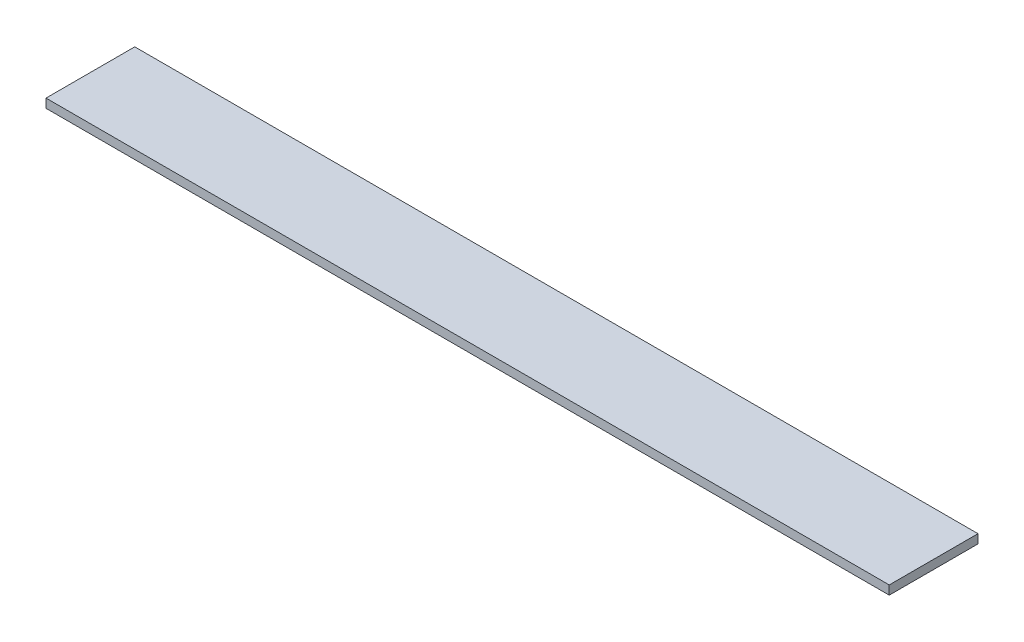
SolidWorks part; units mm, degrees
ref_plane "Face" through (0, 0, 0) normal (0, 0, 1) x (1, 0, 0)
ref_plane "Dessus" through (0, 0, 0) normal (0, 1, 0) x (1, 0, 0)
ref_plane "Droite" through (0, 0, 0) normal (1, 0, 0) x (0, 0, -1)
sketch "Esquisse1" plane through (0, 0, 0) normal (0, 1, 0) x (1, 0, 0)
  line L1 (0, 0) -> (950, 0)
  line L2 (0, 0) -> (0, 100)
  line L3 (0, 100) -> (950, 100)
  line L4 (950, 0) -> (950, 100)
  dimension "D1" = 950
  dimension "D2" = 100
extrude "Extrusion1" add sketch "Esquisse1" along normal blind 10
